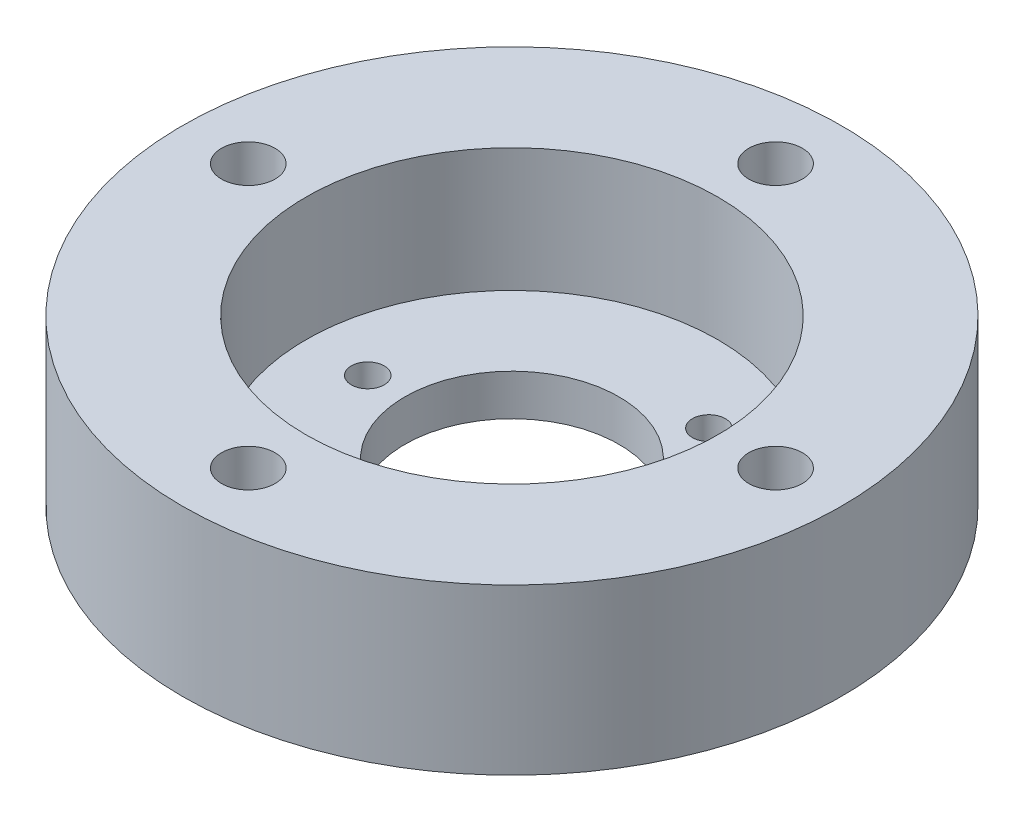
SolidWorks part; units mm, degrees
ref_plane "Front Plane" through (0, 0, 0) normal (0, 0, 1) x (1, 0, 0)
ref_plane "Top Plane" through (0, 0, 0) normal (0, 1, 0) x (1, 0, 0)
ref_plane "Right Plane" through (0, 0, 0) normal (1, 0, 0) x (0, 0, -1)
sketch "Sketch1" plane through (0, 0, 0) normal (0, 0, 1) x (1, 0, 0)
  line L0 (13, 0) -> (13, 5)
  line L1 (13, 5) -> (25, 5)
  line L2 (25, 5) -> (25, 20)
  line L3 (25, 20) -> (40, 20)
  line L4 (40, 20) -> (40, 0)
  line L5 (40, 0) -> (13, 0)
  line L6 (0, 51.3951) -> (0, -36.0117) construction
  dimension "D1" = 13
  dimension "D2" = 25
  dimension "D3" = 20
  dimension "D4" = 5
  dimension "D5" = 0
  dimension "D6" = 40
revolve "Revolve1" add sketch "Sketch1" angle 360 about L6
sketch "Sketch2" plane through (0, 20, 0) normal (0, 1, 0) x (1, 0, 0)
  circle A1 centre (-17.5, 0) radius 2
  circle A3 centre (0, 0) radius 17.5 construction
  dimension "D3" = 4
  dimension "D4" = 35
extrude "Cut-Extrude1" cut sketch "Sketch2" against normal through all
sketch "Sketch3" plane through (0, 20, 0) normal (0, 1, 0) x (1, 0, 0)
  circle A0 centre (0, 32) radius 3.25
  dimension "D1" = 6.5
  dimension "D2" = 32
extrude "Cut-Extrude2" cut sketch "Sketch3" against normal through all
pattern_circular "CirPattern1" count 4 over 360 about axis through (0, 0, 0) along (0, 1, 0) of "Cut-Extrude2"
pattern_circular "CirPattern2" count 3 over 360 about axis through (0, 0, 0) along (0, 1, 0) of "Cut-Extrude1"
